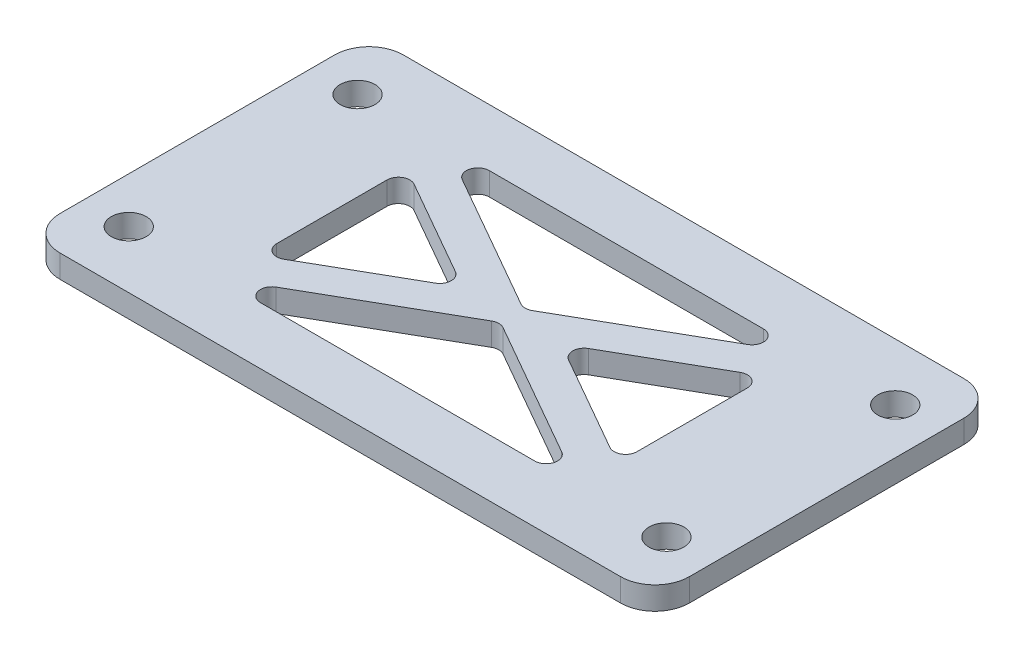
SolidWorks part; units mm, degrees
material "Thornel Mat VMA"
ref_plane "前视基准面" through (0, 0, 0) normal (0, 0, 1) x (1, 0, 0)
ref_plane "上视基准面" through (0, 0, 0) normal (0, 1, 0) x (1, 0, 0)
ref_plane "右视基准面" through (0, 0, 0) normal (1, 0, 0) x (0, 0, -1)
other "Configuration Table"
sketch "草图1" plane through (0, 0, 0) normal (0, 1, 0) x (1, 0, 0)
  line L1 (-27.5, -15) -> (27.5, -15)
  line L2 (-27.5, -15) -> (-27.5, 15)
  line L3 (-27.5, 15) -> (27.5, 15)
  line L4 (27.5, -15) -> (27.5, 15)
  line L5 (-27.5, -15) -> (27.5, 15) construction
  line L6 (-27.5, 15) -> (27.5, -15) construction
  point P0 (0, 0)
  dimension "D1" = 55
  dimension "D2" = 30
extrude "凸台-拉伸1" add sketch "草图1" along normal blind 2
sketch "草图2" plane through (0, 2, 0) normal (0, 1, 0) x (1, 0, 0)
  line L1 (23.5, -10) -> (-23.5, -10) construction
  line L2 (23.5, -10) -> (23.5, 10) construction
  line L3 (23.5, 10) -> (-23.5, 10) construction
  line L4 (-23.5, -10) -> (-23.5, 10) construction
  line L5 (23.5, -10) -> (-23.5, 10) construction
  line L6 (23.5, 10) -> (-23.5, -10) construction
  circle A0 centre (-23.5, 10) radius 1.525
  circle A1 centre (-23.5, -10) radius 1.525
  circle A2 centre (23.5, -10) radius 1.525
  circle A3 centre (23.5, 10) radius 1.525
  point P0 (0, 0)
  dimension "D3" = 3.05
  dimension "D1" = 47
  dimension "D2" = 20
extrude "切除-拉伸1" cut sketch "草图2" against normal blind 2
fillet "圆角1" radius 3 4 edges at (27.5, 1, 15) (-27.5, 1, -15) (27.5, 1, -15) (-27.5, 1, 15)
sketch "草图3" plane through (0, 2, 0) normal (0, 1, 0) x (1, 0, 0)
  line L0 (-15.75, 10) -> (15.75, 10)
  line L1 (-17.5, -10) -> (17.5, -10) construction
  line L2 (-17.5, -10) -> (-17.5, 10) construction
  line L3 (-17.5, 10) -> (17.5, 10) construction
  line L4 (17.5, -10) -> (17.5, 10) construction
  line L5 (-17.5, -10) -> (17.5, 10) construction
  line L6 (-17.5, 10) -> (17.5, -10) construction
  line L7 (15.75, 10) -> (0, 1)
  line L8 (0, 1) -> (-15.75, 10)
  line L9 (-15.75, 6.5447) -> (-15.75, -6.5447)
  line L10 (-15.75, -6.5447) -> (-4.2967, 0)
  line L11 (-4.2967, 0) -> (-15.75, 6.5447)
  line L12 (0, 0) -> (0, -10) construction
  line L13 (0, 0) -> (17.5, 0) construction
  line L14 (-15.75, -10) -> (15.75, -10)
  line L15 (0, -1) -> (-15.75, -10)
  line L16 (15.75, -10) -> (0, -1)
  line L17 (15.75, 6.5447) -> (15.75, -6.5447)
  line L18 (15.75, -6.5447) -> (4.2967, 0)
  line L19 (4.2967, 0) -> (15.75, 6.5447)
  point P0 (0, 0)
  dimension "D1" = 35
  dimension "D2" = 20
  dimension "D3" = 1
  dimension "D4" = 3
extrude "切除-拉伸2" cut sketch "草图3" against normal up to surface (2 mm away) up to face at (23.5, 0, -8.475)
fillet "圆角2" radius 1 12 edges at (0, 1, -1) (-15.75, 1, -10) (15.75, 1, -10) (4.2967, 1, 0) (15.75, 1, 6.5447) (-15.75, 1, 10) (0, 1, 1) (15.75, 1, 10) (15.75, 1, -6.5447) (-15.75, 1, -6.5447) (-15.75, 1, 6.5447) (-4.2967, 1, 0)
